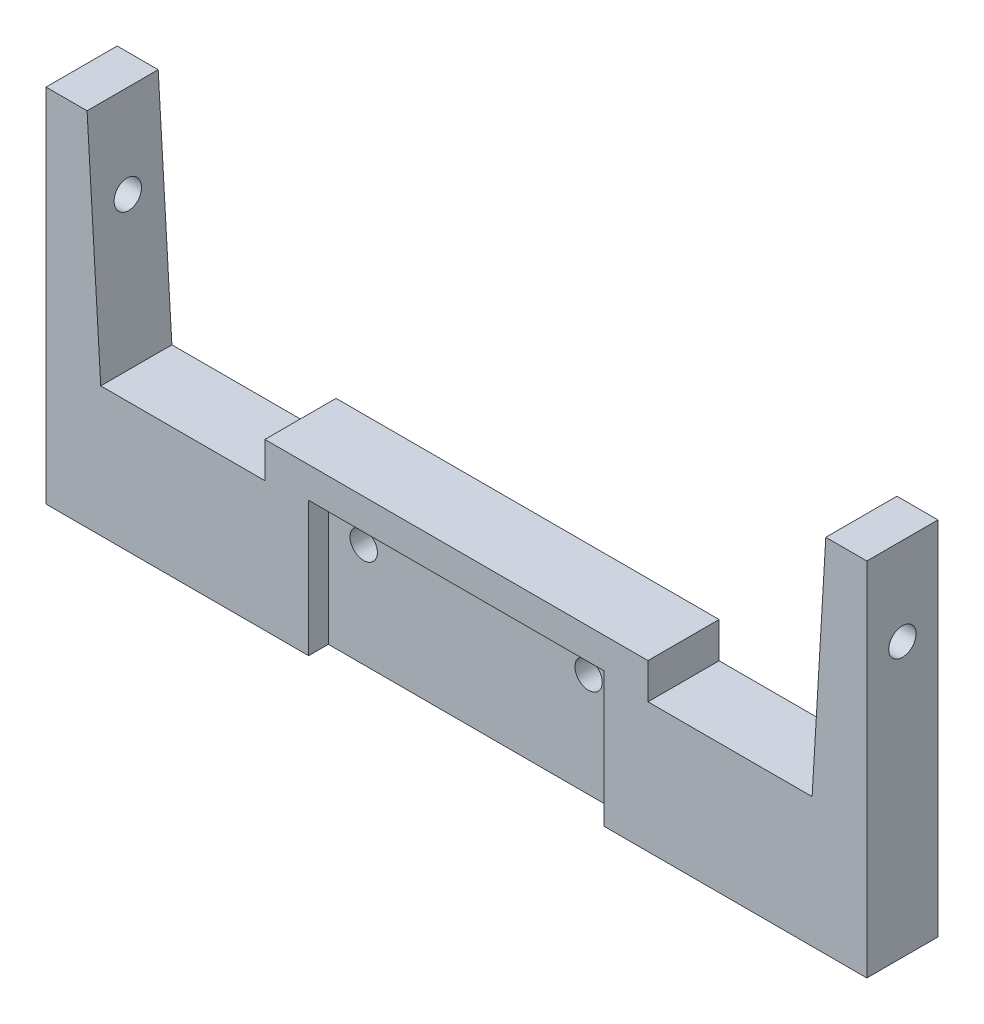
SolidWorks part; units mm, degrees
ref_plane "Piano frontale" through (0, 0, 0) normal (0, 0, 1) x (1, 0, 0)
ref_plane "Piano superiore" through (0, 0, 0) normal (0, 1, 0) x (1, 0, 0)
ref_plane "Piano destro" through (0, 0, 0) normal (1, 0, 0) x (0, 0, -1)
sketch "Schizzo1" plane through (0, 0, 0) normal (0, 0, 1) x (1, 0, 0)
  line L0 (0, 0) -> (75, 0)
  line L1 (75, 0) -> (75, 33)
  line L2 (75, 33) -> (71.25, 33)
  line L3 (71.25, 33) -> (70, 11.8539)
  line L4 (70, 11.8539) -> (55, 11.8539)
  line L5 (55, 11.8539) -> (55, 15.1181)
  line L6 (55, 15.1181) -> (20, 15.1181)
  line L7 (20, 15.1181) -> (20, 11.8539)
  line L8 (20, 11.8539) -> (5, 11.8539)
  line L9 (5, 11.8539) -> (3.75, 33)
  line L10 (3.75, 33) -> (0, 33)
  line L11 (0, 33) -> (0, 0)
  dimension "D1" = 33
  dimension "D2" = 75
  dimension "D3" = 65
  dimension "D4" = 67.5
  dimension "D5" = 3.75
  dimension "D6" = 5
  dimension "D7" = 35
  dimension "D8" = 15
extrude "Estrusione-Estrusione1" add sketch "Schizzo1" along normal blind 6.5
sketch "Schizzo2" plane through (0, 0, 6.5) normal (0, 0, 1) x (1, 0, 0)
  line L0 (20, 15.1181) -> (20, 11.8539) construction
  circle A0 centre (27.225, 9.5) radius 1.25
  circle A1 centre (47.775, 9.5) radius 1.25
  dimension "D1" = 2.5
  dimension "D2" = 20.55
  dimension "D4" = 2.5
  dimension "D3" = 7.225
sketch "Schizzo3" plane through (0, 0, 0) normal (0, 0, -1) x (-1, 0, 0)
  line L1 (-44.5996, 9.5) -> (-46.1873, 12.25)
  line L2 (-46.1873, 12.25) -> (-49.3627, 12.25)
  line L3 (-49.3627, 12.25) -> (-50.9504, 9.5)
  line L4 (-50.9504, 9.5) -> (-49.3627, 6.75)
  line L5 (-49.3627, 6.75) -> (-46.1873, 6.75)
  line L6 (-46.1873, 6.75) -> (-44.5996, 9.5)
  line L7 (-24.0496, 9.5) -> (-25.6373, 12.25)
  line L8 (-25.6373, 12.25) -> (-28.8127, 12.25)
  line L9 (-28.8127, 12.25) -> (-30.4004, 9.5)
  line L10 (-30.4004, 9.5) -> (-28.8127, 6.75)
  line L11 (-28.8127, 6.75) -> (-25.6373, 6.75)
  line L12 (-25.6373, 6.75) -> (-24.0496, 9.5)
  circle A0 centre (-47.775, 9.5) radius 2.75 construction
  circle A1 centre (-27.225, 9.5) radius 2.75 construction
  dimension "D1" = 5.5
  dimension "D2" = 5.5
extrude "Taglio-Estrusione2" cut sketch "Schizzo3" against normal blind 2.5
extrude "Taglio-Estrusione3" cut sketch "Schizzo2" against normal through all
sketch "Schizzo4" plane through (0, 0, 6.5) normal (0, 0, 1) x (1, 0, 0)
  line L0 (0, 0) -> (75, 0) construction
  line L1 (23.9967, 12.3) -> (50.9967, 12.3)
  line L2 (23.9967, 12.3) -> (23.9967, 0)
  line L3 (23.9967, 0) -> (50.9967, 0)
  line L4 (50.9967, 12.3) -> (50.9967, 0)
  dimension "D1" = 27
  dimension "D2" = 12.3
extrude "Taglio-Estrusione4" cut sketch "Schizzo4" against normal blind 1.8
sketch "Schizzo6" plane through (0, 0, 0) normal (-1, 0, 0) x (0, 0, 1)
  line L0 (6.5, 33) -> (0, 33) construction
  line L1 (6.5, 33) -> (6.5, 0) construction
  circle A0 centre (3.25, 25) radius 1.25
  dimension "D3" = 2.5
  dimension "D1" = 8
  dimension "D2" = 3.25
extrude "Taglio-Estrusione5" cut sketch "Schizzo6" against normal through all contours A0
